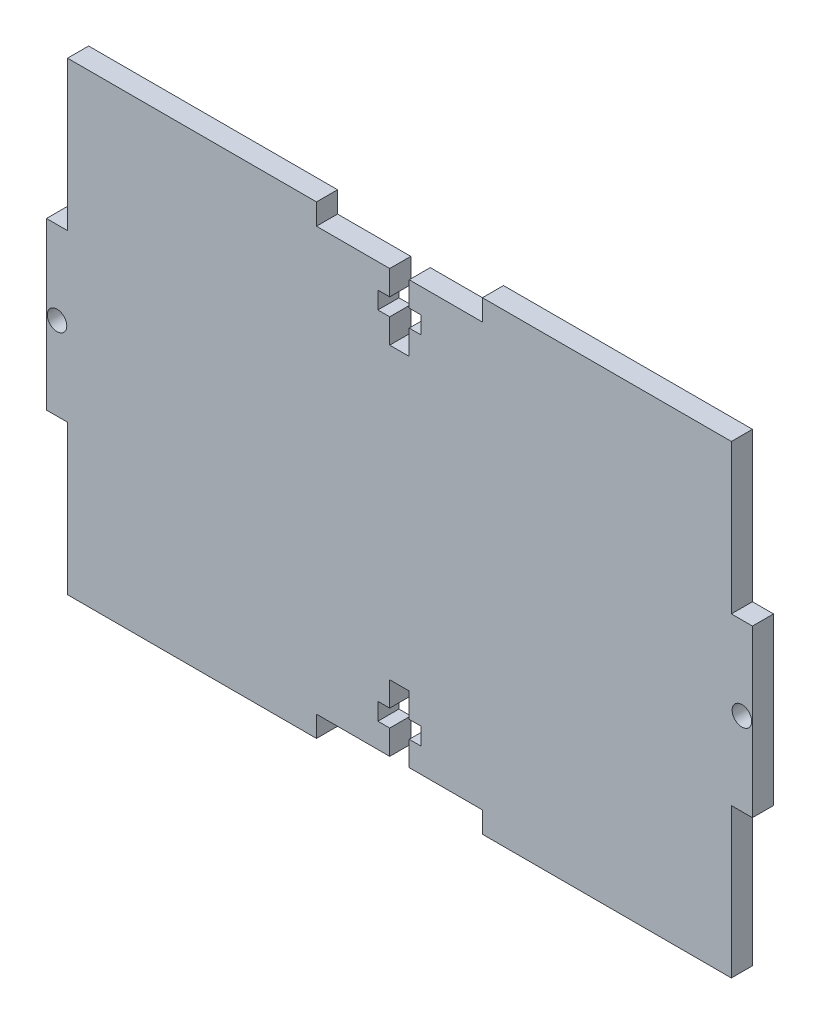
SolidWorks part; units mm, degrees
ref_plane "Front Plane" through (0, 0, 0) normal (0, 0, 1) x (1, 0, 0)
ref_plane "Top Plane" through (0, 0, 0) normal (0, 1, 0) x (1, 0, 0)
ref_plane "Right Plane" through (0, 0, 0) normal (1, 0, 0) x (0, 0, -1)
sketch "Sketch1" plane through (0, 0, 0) normal (0, 0, 1) x (1, 0, 0)
  line L0 (0, 35) -> (0, -35) construction
  line L1 (-50, 35) -> (50, 35)
  line L2 (-50, 35) -> (-50, -35)
  line L3 (-50, -35) -> (50, -35)
  line L4 (50, 35) -> (50, -35)
  line L5 (-50, 35) -> (50, -35) construction
  line L6 (-50, -35) -> (50, 35) construction
  line L7 (-50, 0) -> (50, 0) construction
  line L8 (-3.25, -25.525) -> (3.25, -25.525)
  line L9 (12.5, 35) -> (-12.5, 35)
  line L10 (12.5, 35) -> (12.5, 31.825)
  line L11 (12.5, 31.825) -> (-12.5, 31.825)
  line L12 (-12.5, 35) -> (-12.5, 31.825)
  line L13 (12.5, 35) -> (-12.5, 31.825) construction
  line L14 (12.5, 31.825) -> (-12.5, 35) construction
  line L15 (-1.47, 31.825) -> (1.47, 31.825)
  line L16 (-1.47, 31.825) -> (-1.47, 21.825)
  line L17 (-1.47, 21.825) -> (1.47, 21.825)
  line L18 (1.47, 31.825) -> (1.47, 21.825)
  line L19 (-1.47, 31.825) -> (1.47, 21.825) construction
  line L20 (-1.47, 21.825) -> (1.47, 31.825) construction
  line L21 (-3.25, 28.125) -> (3.25, 28.125)
  line L22 (-3.25, 28.125) -> (-3.25, 25.525)
  line L23 (-3.25, 25.525) -> (3.25, 25.525)
  line L24 (3.25, 28.125) -> (3.25, 25.525)
  line L25 (-3.25, 28.125) -> (3.25, 25.525) construction
  line L26 (-3.25, 25.525) -> (3.25, 28.125) construction
  line L27 (3.25, -28.125) -> (3.25, -25.525)
  line L28 (-3.25, -28.125) -> (3.25, -28.125)
  line L29 (-3.25, -28.125) -> (-3.25, -25.525)
  line L30 (-1.47, -21.825) -> (1.47, -21.825)
  line L31 (1.47, -31.825) -> (1.47, -21.825)
  line L32 (-1.47, -31.825) -> (1.47, -31.825)
  line L33 (-1.47, -31.825) -> (-1.47, -21.825)
  line L34 (12.5, -31.825) -> (-12.5, -31.825)
  line L35 (-12.5, -35) -> (-12.5, -31.825)
  line L36 (12.5, -35) -> (-12.5, -35)
  line L37 (12.5, -35) -> (12.5, -31.825)
  line L38 (53.175, -12.5) -> (50, -12.5)
  line L39 (-53.175, 12.5) -> (-50, 12.5)
  line L40 (-53.175, 12.5) -> (-53.175, -12.5)
  line L41 (-53.175, -12.5) -> (-50, -12.5)
  line L42 (-50, 12.5) -> (-50, -12.5)
  line L43 (-53.175, 12.5) -> (-50, -12.5) construction
  line L44 (-53.175, -12.5) -> (-50, 12.5) construction
  line L45 (50, 12.5) -> (50, -12.5)
  line L46 (53.175, 12.5) -> (50, 12.5)
  line L47 (53.175, 12.5) -> (53.175, -12.5)
  circle A0 centre (-51.5875, 0) radius 1.47
  circle A1 centre (51.5875, 0) radius 1.47
  point P0 (0, 0)
  point P10 (0, 33.4125)
  point P15 (0, 26.825)
  point P20 (0, 26.825)
  point P37 (-51.5875, 0)
  dimension "D11" = 2.94
  dimension "D1" = 70
  dimension "D2" = 100
  dimension "D3" = 3.175
  dimension "D4" = 10
  dimension "D5" = 2.94
  dimension "D6" = 25
  dimension "D7" = 6.5
  dimension "D8" = 2.6
  dimension "D9" = 6.3
  dimension "D10" = 3.175
extrude "Boss-Extrude1" add sketch "Sketch1" along normal mid plane 3.175 contours L21 L24 L23 L18 L17 L16 L22 L11 L12 L1 L2 L3 L4 L10 | L40 L39 L42 L41 | A0 | L38 L45 L46 L47 | A1
